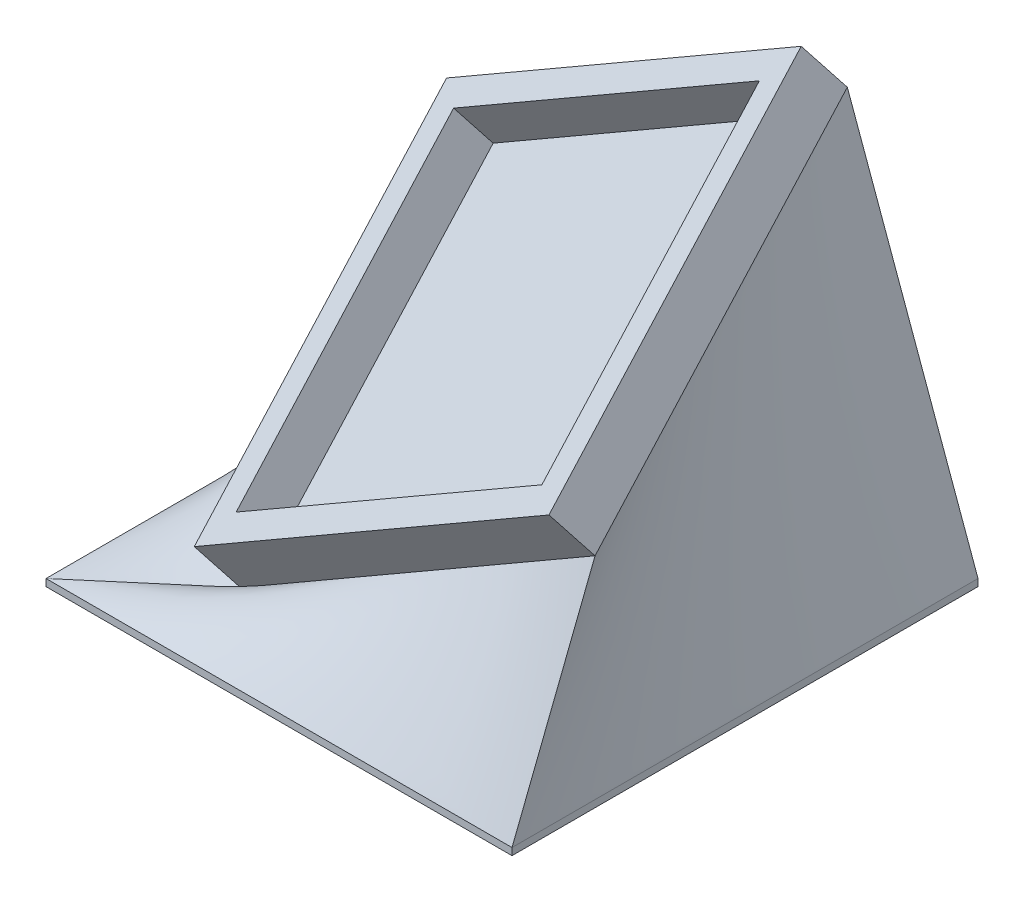
SolidWorks part; units mm, degrees
ref_plane "Front Plane" through (0, 0, 0) normal (0, 0, 1) x (1, 0, 0)
ref_plane "Top Plane" through (0, 0, 0) normal (0, 1, 0) x (1, 0, 0)
ref_plane "Right Plane" through (0, 0, 0) normal (1, 0, 0) x (0, 0, -1)
sketch "Sketch1" plane through (0, 0, 0) normal (0, 1, 0) x (1, 0, 0)
  line L1 (-22.2888, 13.0013) -> (14.5412, 13.0013)
  line L2 (-22.2888, 13.0013) -> (-22.2888, -23.8287)
  line L3 (-22.2888, -23.8287) -> (14.5412, -23.8287)
  line L4 (14.5412, 13.0013) -> (14.5412, -23.8287)
  dimension "D1" = 36.83
  dimension "D2" = 36.83
extrude "Boss-Extrude1" add sketch "Sketch1" along normal blind 0.635
sketch "Sketch2" plane through (0, 0.635, 0) normal (0, 1, 0) x (1, 0, 0)
  line L0 (14.5412, 13.0013) -> (-22.2888, 13.0013) construction
  line L1 (-19.7488, 10.4613) -> (12.0012, 10.4613)
  line L2 (-19.7488, 10.4613) -> (-19.7488, -21.2887)
  line L3 (-19.7488, -21.2887) -> (12.0012, -21.2887)
  line L4 (12.0012, 10.4613) -> (12.0012, -21.2887)
  line L5 (-22.2888, 13.0013) -> (-22.2888, -23.8287) construction
  line L7 (-22.2888, 13.0013) -> (14.5412, 13.0013)
  line L8 (-22.2888, 13.0013) -> (-22.2888, -23.8287)
  line L9 (-22.2888, -23.8287) -> (14.5412, -23.8287)
  line L10 (14.5412, 13.0013) -> (14.5412, -23.8287)
  dimension "D1" = 31.75
  dimension "D2" = 31.75
  dimension "D3" = 2.54
  dimension "D4" = 2.54
extrude "Boss-Extrude2" add sketch "Sketch2" along normal blind 3.81 contours L8 L7 L10 L9 | L2 L1 L4 L3
move or copy body "Body-Move/Copy1" bodies to move or copy 102 copy no translate (0, 22.86, 0)
sketch "Sketch3" plane through (0, 0, 0) normal (0, 1, 0) x (1, 0, 0)
  line L0 (-22.2888, 13.0013) -> (-22.2888, -23.8287) construction
  line L1 (-24.8288, 15.5413) -> (17.0812, 15.5413)
  line L2 (-24.8288, 15.5413) -> (-24.8288, -26.3687)
  line L3 (-24.8288, -26.3687) -> (17.0812, -26.3687)
  line L4 (17.0812, 15.5413) -> (17.0812, -26.3687)
  line L5 (-22.2888, -23.8287) -> (14.5412, -23.8287) construction
  dimension "D1" = 41.91
  dimension "D2" = 41.91
  dimension "D3" = 2.54
  dimension "D4" = 2.54
extrude "Boss-Extrude3" add sketch "Sketch3" along normal blind 0.635 separate body
move or copy body "Body-Move/Copy2" bodies to move or copy 103 copy no rotation origin (-5.233, 4.3983, 4.0545) rotation axis (0.6947, 0.1862, 0.6947) rotation angle 42.181
move or copy body "Body-Move/Copy3" bodies to move or copy 105 copy no translate (8.1875, 0, -11.5631)
loft "Loft2" add section face at (-3.5227, 18.3356, 2.8994) section face at (-3.8738, 0.635, 5.4137)
sketch "Sketch7" plane through (-6.1811, 10.7059, -21.4119) normal (-0.25, 0.433, -0.866) x (-0.9682, -0.1118, 0.2236)
  text T0 "30 x 30"
extrude "Cut-Extrude4" cut sketch "Sketch7" against normal blind 0.635
